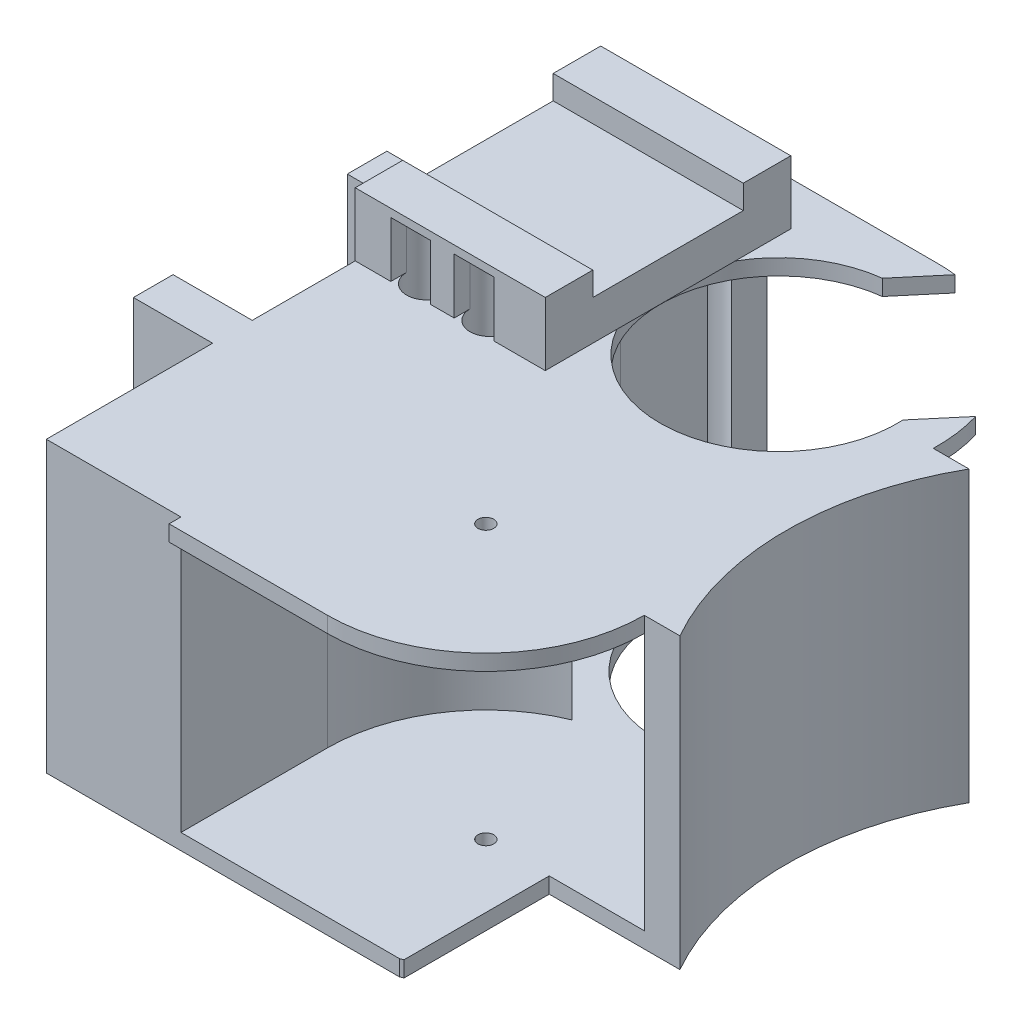
SolidWorks part; units mm, degrees
ref_plane "Front" through (0, 0, 0) normal (0, 0, 1) x (1, 0, 0)
ref_plane "Top" through (0, 0, 0) normal (0, 1, 0) x (1, 0, 0)
ref_plane "Right" through (0, 0, 0) normal (1, 0, 0) x (0, 0, -1)
sketch "Sketch1" plane through (0, 0, 0) normal (0, 1, 0) x (1, 0, 0)
  line L0 (45, 0) -> (45, 18.5)
  line L1 (0, 0) -> (45, 0)
  line L2 (0, 0) -> (0, 21)
  line L3 (0, 74) -> (22, 74)
  line L4 (0, 26) -> (-10, 26)
  line L5 (45, 18.5) -> (61.5, 18.5)
  line L6 (-10, 26) -> (-10, 21)
  line L7 (51.9917, 55) -> (61.5, 55)
  line L8 (22, 55.5) -> (22, 74)
  line L9 (-10, 21) -> (0, 21)
  line L10 (0, 48) -> (-10, 48)
  line L11 (-10, 48) -> (-10, 53)
  line L12 (-10, 53) -> (0, 53)
  line L13 (0, 53) -> (0, 74)
  line L14 (0, 26) -> (0, 48)
  line L15 (17, 18.5) -> (17, 0)
  line L16 (17, 55.5) -> (17, 74)
  circle A1 centre (7, 68) radius 2
  circle A2 centre (15, 68) radius 2.5
  circle A3 centre (7, 40) radius 2
  circle A4 centre (15, 40) radius 2
  arc A5 (57, 18.5) -> (44.5993, 37) centre (37, 18.5) ccw
  arc A6 (22, 55.5) -> (51.9917, 55) centre (37, 55.5) ccw
  arc A7 (61.5, 55) -> (61.5, 18.5) centre (93.686, 36.75) ccw
  circle A8 centre (37, 18.5) radius 1
  arc A9 (17, 55.5) -> (29.4007, 37) centre (37, 55.5) ccw
  arc A10 (44.5993, 0) -> (45, 0.1697) centre (37, 18.5) ccw
  arc A11 (44.5993, 37) -> (56.9937, 55) centre (37, 55.5) ccw
  arc A12 (29.4007, 37) -> (17, 18.5) centre (37, 18.5) ccw
extrude "Boss-Extrude18" add sketch "Sketch1" along normal blind 34.5 contours A12 A9 L16 A2 L3 L13 L12 L11 L10 L14 L4 L6 L9 L2 L1 L15 A4 A3 A1 | A11 A5 L5 A7 L7 | A9 A12 L15 L1 A10 L0 L5 A5 A11 L7 A6 L8 L3 L16 A2 A8
sketch "Sketch7" plane through (0, 34.5, 0) normal (0, 1, 0) x (1, 0, 0)
  line L0 (17, 55.5) -> (17, 75.5)
  line L1 (17, 75.5) -> (37, 75.5)
  line L2 (17, 18.5) -> (17, -1.5)
  line L3 (17, -1.5) -> (37, -1.5)
  arc A0 (37, -1.5) -> (44.5993, 37) centre (37, 18.5) ccw
  arc A1 (17, 55.5) -> (29.4007, 37) centre (37, 55.5) ccw
  arc A2 (29.4007, 37) -> (17, 18.5) centre (37, 18.5) ccw
  arc A3 (44.5993, 37) -> (37, 75.5) centre (37, 55.5) ccw
extrude "Cut-Extrude16" cut sketch "Sketch7" against normal blind 32.5
sketch "Sketch8" plane through (0, 34.5, 0) normal (0, 1, 0) x (1, 0, 0)
  line L0 (17, 18.5) -> (17, -1.5)
  line L1 (17, -1.5) -> (37, -1.5)
  line L2 (17, 55.5) -> (17, 75.5)
  line L3 (17, 75.5) -> (37, 75.5)
  arc A0 (29.4007, 37) -> (17, 18.5) centre (37, 18.5) ccw
  arc A1 (44.5993, 37) -> (37, 75.5) centre (37, 55.5) ccw
  arc A2 (37, -1.5) -> (44.5993, 37) centre (37, 18.5) ccw
  arc A3 (17, 55.5) -> (29.4007, 37) centre (37, 55.5) ccw
extrude "Boss-Extrude21" add sketch "Sketch8" against normal blind 2
sketch "Sketch9" plane through (0, 34.5, 0) normal (0, 1, 0) x (1, 0, 0)
  line L0 (24, 68) -> (0, 68)
  line L1 (24, 68) -> (24, 40)
  line L2 (24, 40) -> (0, 40)
  line L3 (0, 26) -> (0, 48) construction
  circle A0 centre (7, 40) radius 2
  circle A1 centre (15, 40) radius 2
extrude "Boss-Extrude22" add sketch "Sketch9" against normal blind 34.5 contours A0
sketch "Sketch10" plane through (0, 34.5, 0) normal (0, 1, 0) x (1, 0, 0)
  circle A0 centre (15, 40) radius 2
extrude "Boss-Extrude23" add sketch "Sketch10" against normal blind 34.5
sketch "Sketch11" plane through (0, 34.5, 0) normal (0, 1, 0) x (1, 0, 0)
  circle A0 centre (7, 41) radius 2
  circle A1 centre (15, 41) radius 2
extrude "Cut-Extrude17" cut sketch "Sketch11" against normal blind 34.5
sketch "Sketch12" plane through (0, 34.5, 0) normal (0, 1, 0) x (1, 0, 0)
  line L0 (0, 68) -> (24, 68)
  line L1 (24, 68) -> (24, 41)
  line L2 (24, 41) -> (0, 41)
  line L3 (0, 26) -> (0, 48) construction
  line L4 (0, 41) -> (0, 68)
extrude "Boss-Extrude24" add sketch "Sketch12" along normal blind 8
sketch "Sketch13" plane through (0, 42.5, 0) normal (0, 1, 0) x (1, 0, 0)
  line L0 (24, 45) -> (0, 45)
  line L1 (24, 41) -> (24, 68) construction
  line L2 (0, 68) -> (0, 41) construction
  line L3 (24, 64) -> (0, 64)
  line L4 (0, 45) -> (0, 64)
  line L5 (24, 45) -> (24, 64)
sketch "Sketch15" plane through (0, 42.5, 0) normal (0, 1, 0) x (1, 0, 0)
extrude "Cut-Extrude18" cut sketch "Sketch13" against normal blind 3
sketch "Sketch16" plane through (0, 0, 0) normal (0, -1, 0) x (-1, 0, 0)
  circle A1 centre (-7, 68) radius 2.5
extrude "Cut-Extrude21" cut sketch "Sketch16" against normal blind 41.5
sketch "Sketch20" plane through (0, 0, 0) normal (0, -1, 0) x (-1, 0, 0)
  circle A0 centre (-15, 68) radius 2.5
extrude "Cut-Extrude22" cut sketch "Sketch20" against normal blind 41.5
sketch "Sketch21" plane through (0, 0, 0) normal (0, -1, 0) x (-1, 0, 0)
  circle A0 centre (-7, 41) radius 2.5
extrude "Cut-Extrude23" cut sketch "Sketch21" against normal blind 41.5
sketch "Sketch22" plane through (0, 0, 0) normal (0, -1, 0) x (-1, 0, 0)
  circle A0 centre (-15, 41) radius 2.5
extrude "Cut-Extrude24" cut sketch "Sketch22" against normal blind 41.5
sketch "Sketch23" plane through (0, 0, -68) normal (0, 0, -1) x (-1, 0, 0)
  line L0 (-24, 39.5952) -> (-24, 42.5)
  line L1 (-24, 42.5) -> (-24, 34.5) construction
  line L14 (-17.5, 41.5) -> (-12.5, 41.5)
  line L15 (-12.5, 41.5) -> (-12.5, 34.5)
  line L16 (-12.5, 34.5) -> (-9.5, 34.5)
  line L17 (-9.5, 34.5) -> (-9.5, 41.5)
  line L18 (-9.5, 41.5) -> (-4.5, 41.5)
  line L19 (-4.5, 41.5) -> (-4.5, 34.5)
  line L20 (-4.5, 34.5) -> (0, 34.5)
  line L21 (0, 34.5) -> (0, 42.5)
  line L22 (0, 42.5) -> (-24, 42.5)
  line L23 (-24, 42.5) -> (-24, 34.5)
  line L24 (-24, 34.5) -> (-17.5, 34.5)
  line L25 (-17.5, 34.5) -> (-17.5, 41.5)
  line L26 (-17.5, 41.5) -> (-12.5, 41.5)
  line L27 (-12.5, 41.5) -> (-12.5, 34.5)
  line L28 (-12.5, 34.5) -> (-9.5, 34.5)
  line L29 (-9.5, 34.5) -> (-9.5, 41.5)
  line L30 (-9.5, 41.5) -> (-4.5, 41.5)
  line L31 (-4.5, 41.5) -> (-4.5, 34.5)
  line L32 (-4.5, 34.5) -> (0, 34.5)
  line L33 (0, 34.5) -> (0, 42.5)
  line L34 (0, 42.5) -> (-24, 42.5)
  line L35 (-24, 39.5952) -> (-24, 34.5)
  line L36 (-24, 34.5) -> (-17.5, 34.5)
  line L37 (-17.5, 34.5) -> (-17.5, 41.5)
  dimension "D1" = 0
extrude "Boss-Extrude25" add sketch "Sketch23" along normal blind 2
sketch "Sketch25" plane through (0, 0, -41) normal (0, 0, 1) x (1, 0, 0)
sketch "Sketch26" plane through (0, 0, -41) normal (0, 0, 1) x (1, 0, 0)
  line L0 (19.8714, 42.5) -> (24, 42.5)
  line L1 (0, 42.5) -> (24, 42.5) construction
  line L2 (24, 42.5) -> (24, 34.5)
  line L3 (24, 34.5) -> (17.5, 34.5)
  line L4 (17.5, 34.5) -> (17.5, 41.5)
  line L5 (17.5, 41.5) -> (12.5, 41.5)
  line L6 (12.5, 41.5) -> (12.5, 34.5)
  line L7 (12.5, 34.5) -> (9.5, 34.5)
  line L8 (9.5, 34.5) -> (9.5, 41.5)
  line L9 (9.5, 41.5) -> (4.5, 41.5)
  line L10 (4.5, 41.5) -> (4.5, 34.5)
  line L11 (4.5, 34.5) -> (0, 34.5)
  line L12 (0, 34.5) -> (0, 42.5)
  line L13 (0, 42.5) -> (19.8714, 42.5)
extrude "Boss-Extrude26" add sketch "Sketch26" along normal blind 2
sketch "Sketch27" plane through (0, 0, -53) normal (0, 0, -1) x (-1, 0, 0)
  circle A0 centre (5, 8.75) radius 1
  circle A1 centre (5, 25.75) radius 1
extrude "Cut-Extrude27" cut sketch "Sketch27" against normal blind 5
sketch "Sketch28" plane through (0, 0, -26) normal (0, 0, -1) x (-1, 0, 0)
  circle A0 centre (5, 8.75) radius 1
  circle A1 centre (5, 25.75) radius 1
extrude "Cut-Extrude28" cut sketch "Sketch28" against normal blind 5
sketch "Sketch29" plane through (0, 32.5, 0) normal (0, -1, 0) x (1, 0, 0)
  circle A0 centre (37, -55.5) radius 15
extrude "Cut-Extrude29" cut sketch "Sketch29" against normal blind 2
sketch "Sketch30" plane through (0, 32.5, 0) normal (0, -1, 0) x (-1, 0, 0)
  circle A0 centre (-37, 18.5) radius 1
extrude "Cut-Extrude30" cut sketch "Sketch30" against normal blind 2
sketch "Sketch31" plane through (0, 34.5, 0) normal (0, 1, 0) x (1, 0, 0)
  line L0 (45.4038, 48.4023) -> (28.5962, 62.5977)
  line L1 (28.5962, 62.5977) -> (39.3739, 75.3586)
  line L2 (45.4038, 48.4023) -> (56.1814, 61.1633)
  arc A1 (56.9937, 55) -> (37, 75.5) centre (37, 55.5) ccw construction
extrude "Cut-Extrude31" cut sketch "Sketch31" against normal blind 10 and the other way through all
sketch "Sketch32" plane through (0, 0, 0) normal (0, -1, 0) x (-1, 0, 0)
  line L0 (0, 74) -> (0, 53)
  line L1 (0, 53) -> (10, 53)
  line L2 (10, 53) -> (10, 48)
  line L3 (10, 48) -> (0, 48)
  line L4 (0, 48) -> (0, 26)
  line L5 (0, 26) -> (10, 26)
  line L6 (10, 26) -> (10, 21)
  line L7 (10, 21) -> (0, 21)
  line L8 (0, 21) -> (0, 0)
  line L9 (0, 0) -> (-44.5993, 0)
  line L10 (-45, 0.1697) -> (-45, 18.5)
  line L11 (-45, 18.5) -> (-61.5, 18.5)
  line L12 (0, 0) -> (-44.5993, 0) construction
  line L13 (-44.5993, 0) -> (-45, 0.1697)
  line L14 (-61.5, 18.5) -> (-61.5, 55)
  line L15 (-22, 55.5) -> (-51.9917, 55)
  line L17 (-61.5, 55) -> (-51.9917, 55)
  line L28 (-22, 55.5) -> (-22, 74)
  line L29 (-22, 74) -> (0, 74)
  circle A0 centre (-7, 68) radius 2.5
  circle A1 centre (-7, 41) radius 2.5
  circle A2 centre (-15, 68) radius 2.5
  circle A3 centre (-15, 41) radius 2.5
  circle A4 centre (-37, 18.5) radius 1
extrude "Boss-Extrude28" add sketch "Sketch32" along normal blind 2
sketch "Sketch34" plane through (0, -2, 0) normal (0, -1, 0) x (-1, 0, 0)
  line L0 (-61.5, 18.5) -> (-45, 18.5) construction
  line L1 (-61.5, 55) -> (-61.5, 18.5) construction
  line L2 (-61.5, 55) -> (-61.5, 18.5)
  arc A0 (-61.5, 55) -> (-61.5, 18.5) centre (-93.686, 36.75) cw
extrude "Cut-Extrude32" cut sketch "Sketch34" against normal blind 2
sketch "Sketch35" plane through (0, -2, 0) normal (0, -1, 0) x (-1, 0, 0)
  line L0 (-22, 55.5) -> (-51.9917, 55) construction
  circle A0 centre (-36.9968, 55.25) radius 15
extrude "Cut-Extrude33" cut sketch "Sketch35" against normal blind 2
sketch "Sketch36" plane through (0, -2, 0) normal (0, -1, 0) x (-1, 0, 0)
  line L0 (-17, 55.5) -> (-17, 74)
  line L1 (0, 74) -> (-22, 74) construction
  line L3 (-17, 74) -> (-37, 75.5)
  arc A0 (-34.0168, 75.2763) -> (-17, 55.5) centre (-37, 55.5) ccw
  circle A1 centre (-15, 68) radius 2.5
extrude "Boss-Extrude30" add sketch "Sketch36" against normal blind 2 from offset 2 contours A1 offset against normal yes
sketch "Sketch38" plane through (0, -2, 0) normal (0, -1, 0) x (1, 0, 0)
  line L0 (17, -75.5) -> (57, -75.5)
  line L1 (17, -55.5) -> (17, -75.5)
  line L2 (57, -75.5) -> (57, -55.5)
  arc A1 (57, -55.5) -> (17, -55.5) centre (37, -55.5) ccw
extrude "Cut-Extrude40" cut sketch "Sketch38" against normal blind 2 from offset 2 offset against normal yes
sketch "Sketch39" plane through (0, 0, 0) normal (0, -1, 0) x (-1, 0, 0)
  circle A0 centre (-15, 68) radius 2.5
extrude "Cut-Extrude41" cut sketch "Sketch39" against normal blind 2
sketch "Sketch41" plane through (0, -2, 0) normal (0, -1, 0) x (-1, 0, 0)
  line L0 (-17, 18.5) -> (-17, -1.5)
  line L1 (-17, -1.5) -> (-37, -1.5)
  line L2 (-37, -1.5) -> (-57, -1.5)
  line L3 (-57, -1.5) -> (-57, 18.5)
  arc A0 (-17, 18.5) -> (-57, 18.5) centre (-37, 18.5) ccw
extrude "Cut-Extrude42" cut sketch "Sketch41" against normal blind 2 from offset 2 offset against normal yes
sketch "Sketch42" plane through (0, 0, -26) normal (0, 0, -1) x (-1, 0, 0)
  circle A0 centre (5, 8.75) radius 1
extrude "Boss-Extrude31" add sketch "Sketch42" against normal blind 5
sketch "Sketch43" plane through (0, 0, -26) normal (0, 0, -1) x (-1, 0, 0)
  circle A0 centre (5, 8.25) radius 1
extrude "Cut-Extrude44" cut sketch "Sketch43" against normal blind 5
sketch "Sketch46" plane through (0, 0, -26) normal (0, 0, -1) x (-1, 0, 0)
  circle A0 centre (5, 25.75) radius 1
extrude "Boss-Extrude32" add sketch "Sketch46" against normal blind 5
sketch "Sketch47" plane through (0, 0, -26) normal (0, 0, -1) x (-1, 0, 0)
  circle A0 centre (5, 24.25) radius 1
extrude "Cut-Extrude45" cut sketch "Sketch47" against normal blind 5
sketch "Sketch48" plane through (0, 0, -53) normal (0, 0, -1) x (-1, 0, 0)
  circle A0 centre (5, 8.75) radius 1
extrude "Boss-Extrude33" add sketch "Sketch48" against normal blind 5
sketch "Sketch49" plane through (0, 0, -53) normal (0, 0, -1) x (-1, 0, 0)
  circle A0 centre (5, 8.25) radius 1
extrude "Cut-Extrude46" cut sketch "Sketch49" against normal blind 5
sketch "Sketch50" plane through (0, 0, -53) normal (0, 0, -1) x (-1, 0, 0)
  circle A0 centre (5, 25.75) radius 1
extrude "Boss-Extrude34" add sketch "Sketch50" against normal blind 5
sketch "Sketch51" plane through (0, 0, -53) normal (0, 0, -1) x (-1, 0, 0)
  circle A0 centre (5, 24.25) radius 1
extrude "Cut-Extrude47" cut sketch "Sketch51" against normal blind 5
ref_plane "Plane1" through (61.5, 0, 0) normal (1, 0, 0) x (0, 0, -1)
